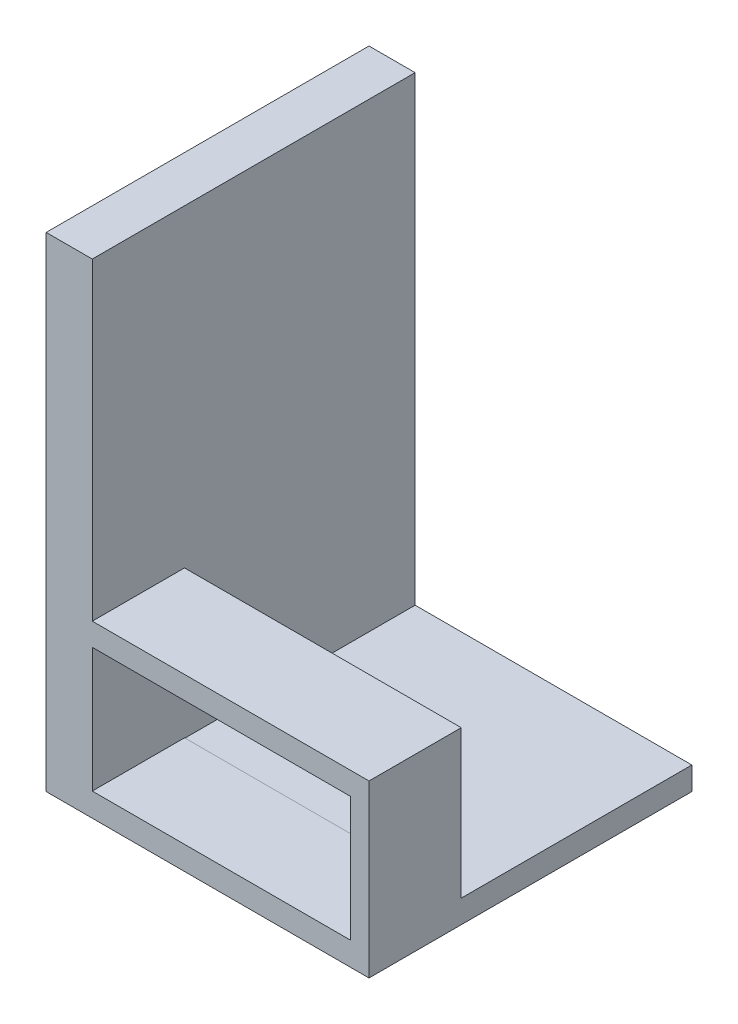
SolidWorks part; units mm, degrees
ref_plane "Front Plane" through (0, 0, 0) normal (0, 0, 1) x (1, 0, 0)
ref_plane "Top Plane" through (0, 0, 0) normal (0, 1, 0) x (1, 0, 0)
ref_plane "Right Plane" through (0, 0, 0) normal (1, 0, 0) x (0, 0, -1)
sketch "Sketch1" plane through (0, 0, 0) normal (0, 1, 0) x (1, 0, 0)
  line L1 (0, 0) -> (35, 0)
  line L2 (0, 0) -> (0, 35)
  line L3 (0, 35) -> (35, 35)
  line L4 (35, 0) -> (35, 35)
  dimension "D1" = 35
  dimension "D2" = 35
extrude "Boss-Extrude1" add sketch "Sketch1" along normal blind 2.5
sketch "Sketch2" plane through (0, 2.5, 0) normal (0, 1, 0) x (1, 0, 0)
  line L0 (0, 0) -> (35, 0) construction
  line L1 (0, 35) -> (5, 35)
  line L2 (0, 35) -> (0, 0)
  line L3 (0, 0) -> (5, 0)
  line L4 (5, 35) -> (5, 0)
  dimension "D1" = 5
extrude "Boss-Extrude2" add sketch "Sketch2" along normal blind 50
sketch "Sketch5" plane through (0, 0, 0) normal (-1, 0, 0) x (0, 0, 1)
  line L0 (-35, 52.5) -> (0, 52.5) construction
  line L1 (-26.0539, 47.5) -> (-9.0539, 47.5)
  line L2 (-26.0539, 47.5) -> (-26.0539, 12.5)
  line L3 (-26.0539, 12.5) -> (-9.0539, 12.5)
  line L4 (-9.0539, 47.5) -> (-9.0539, 12.5)
  dimension "D1" = 17
  dimension "D2" = 35
  dimension "D3" = 5
extrude "Cut-Extrude2" cut sketch "Sketch5" against normal blind 4
sketch "Sketch6" plane through (0, 2.5, 0) normal (0, 1, 0) x (1, 0, 0)
  line L0 (35, 0) -> (35, 35) construction
  line L1 (5, 0) -> (35, 0)
  line L2 (5, 0) -> (5, 10)
  line L3 (5, 10) -> (35, 10)
  line L4 (35, 0) -> (35, 10)
  dimension "D1" = 10
extrude "Boss-Extrude3" add sketch "Sketch6" along normal blind 16
sketch "Sketch7" plane through (0, 0, 0) normal (0, 0, 1) x (1, 0, 0)
  line L0 (35, 18.5) -> (35, 0) construction
  line L1 (33, 2.55) -> (5, 2.55)
  line L2 (33, 2.55) -> (33, 16.05)
  line L3 (33, 16.05) -> (5, 16.05)
  line L4 (5, 2.55) -> (5, 16.05)
  line L5 (0, 0) -> (35, 0) construction
  dimension "D1" = 28
  dimension "D2" = 13.5
  dimension "D3" = 2
  dimension "D4" = 2.55
extrude "Cut-Extrude3" cut sketch "Sketch7" against normal blind 16
